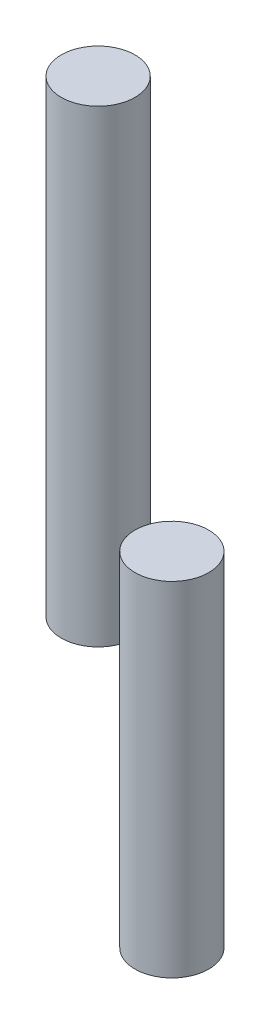
SolidWorks part; units mm, degrees
ref_plane "Front Plane" through (0, 0, 0) normal (0, 0, 1) x (1, 0, 0)
ref_plane "Top Plane" through (0, 0, 0) normal (0, 1, 0) x (1, 0, 0)
ref_plane "Right Plane" through (0, 0, 0) normal (1, 0, 0) x (0, 0, -1)
sketch "Sketch1" plane through (0, 0, 0) normal (0, 1, 0) x (1, 0, 0)
  circle A0 centre (0, 0) radius 30
  dimension "D1" = 60
extrude "Boss-Extrude1" add sketch "Sketch1" along normal blind 381
sketch "Sketch2" plane through (0, 0, 0) normal (0, -1, 0) x (1, 0, 0)
  circle A0 centre (60, 0) radius 30
  circle A1 centre (0, 0) radius 30 construction
  dimension "D1" = 60
extrude "Boss-Extrude2" add sketch "Sketch2" along normal blind 203.2 and the other way blind 76.2 separate body
